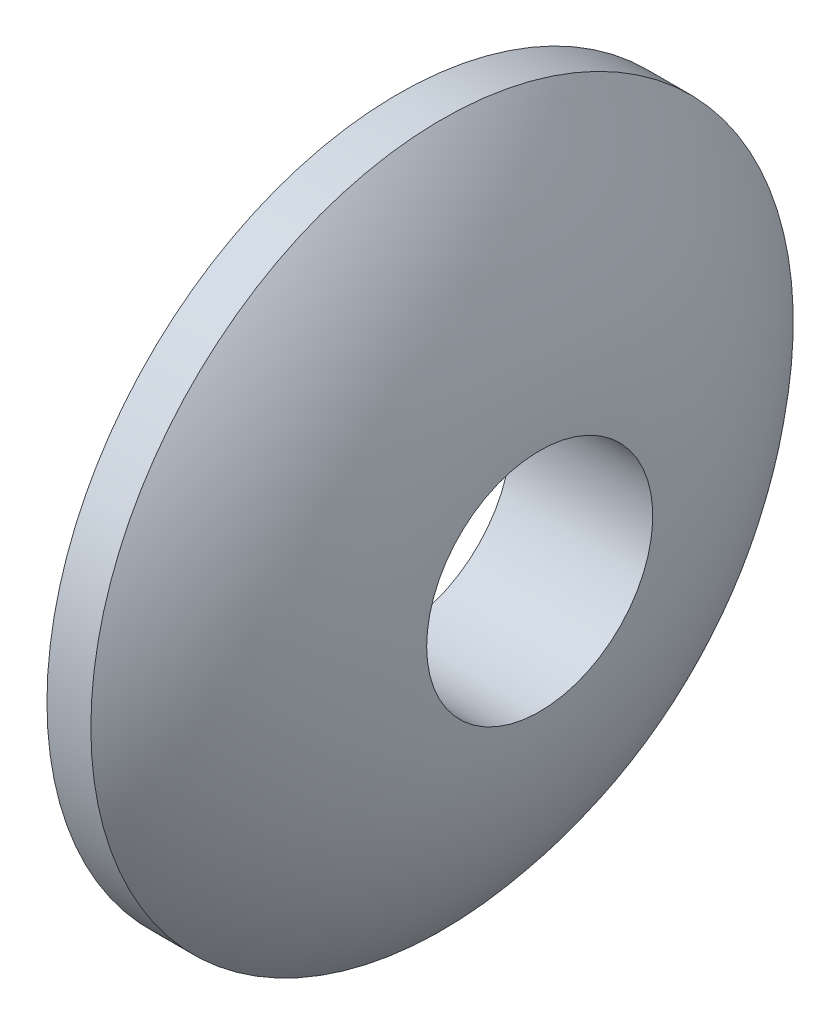
SolidWorks part; units mm, degrees
ref_plane "Front Plane" through (0, 0, 0) normal (0, 0, 1) x (1, 0, 0)
ref_plane "Top Plane" through (0, 0, 0) normal (0, 1, 0) x (1, 0, 0)
ref_plane "Right Plane" through (0, 0, 0) normal (1, 0, 0) x (0, 0, -1)
sketch "Sketch1" plane through (0, 0, 0) normal (0, 0, 1) x (1, 0, 0)
  line L1 (0, 0) -> (0, 8)
  line L2 (-6.0422, 0) -> (8.9789, 0) construction
  line L3 (0, 8) -> (1, 8)
  line L4 (0, 0) -> (3, 0)
  arc A0 (1, 8) -> (3, 0) centre (-5.7611, 2.0597) cw
  dimension "D3" = 1
  dimension "D2" = 3
  dimension "D4" = 9
  dimension "D1" = 8
revolve "Revolve1" add sketch "Sketch1" angle 360 about L2
sketch "Sketch2" plane through (0, 0, 0) normal (-1, 0, 0) x (0, 0, 1)
  circle A0 centre (0, 0) radius 2.575
  dimension "D1" = 5.15
extrude "Cut-Extrude1" cut sketch "Sketch2" against normal through all
